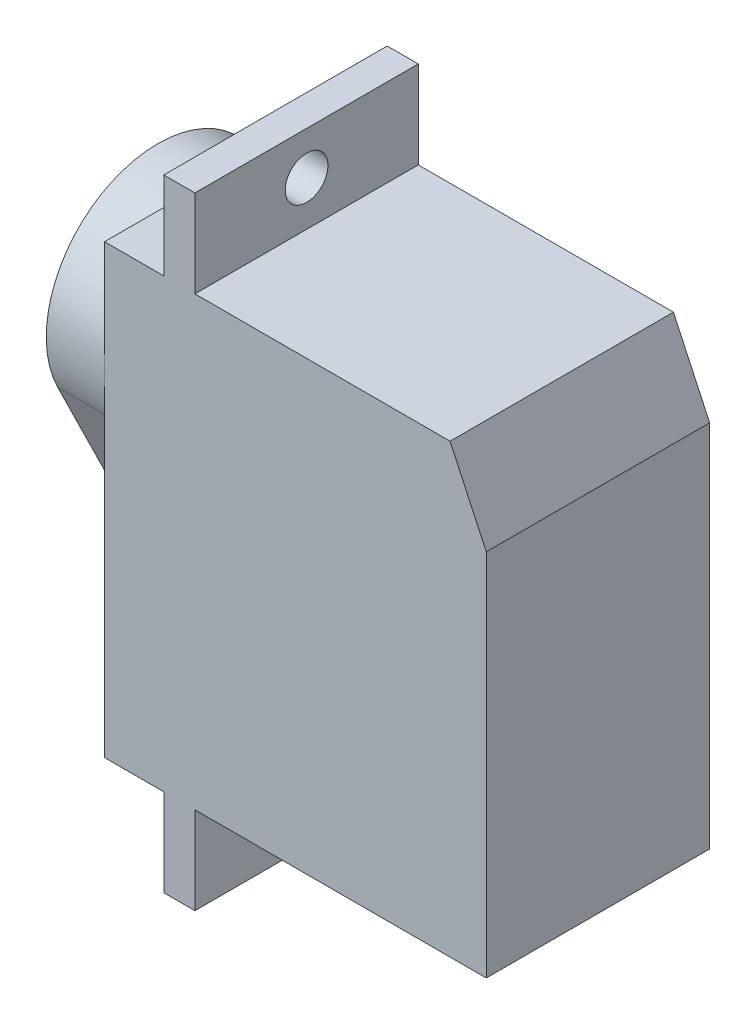
SolidWorks part; units mm, degrees
material "聚亚安酯(11671)"
ref_plane "前视基准面" through (0, 0, 0) normal (0, 0, 1) x (1, 0, 0)
ref_plane "上视基准面" through (0, 0, 0) normal (0, 1, 0) x (1, 0, 0)
ref_plane "右视基准面" through (0, 0, 0) normal (1, 0, 0) x (0, 0, -1)
sketch "草图1" plane through (0, 0, 0) normal (0, 0, 1) x (1, 0, 0)
  line L0 (4.65, 23) -> (4.65, 27.5)
  line L1 (0, 0) -> (3.05, 0)
  line L2 (0, 0) -> (0, 23)
  line L3 (0, 23) -> (3.05, 23)
  line L4 (19.65, 0) -> (19.65, 23)
  line L5 (4.65, -4.5) -> (3.05, -4.5)
  line L6 (4.65, -4.5) -> (4.65, 0)
  line L7 (4.65, 27.5) -> (3.05, 27.5)
  line L8 (3.05, -4.5) -> (3.05, 0)
  line L9 (3.05, 23) -> (3.05, 27.5)
  line L10 (4.65, 0) -> (19.65, 0)
  line L11 (4.65, 23) -> (19.65, 23)
  point P4 (3.85, 11.5)
  dimension "D1" = 19.65
  dimension "D2" = 23
  dimension "D3" = 11.5
  dimension "D4" = 15
  dimension "D5" = 1.6
  dimension "D6" = 32
extrude "凸台-拉伸1" add sketch "草图1" along normal blind 11.5
sketch "草图2" plane through (0, 0, 0) normal (0, 0, 1) x (1, 0, 0)
  line L0 (-4.0495, 11.5) -> (24.7018, 11.5) construction
  line L1 (19.65, 23) -> (4.65, 23) construction
  dimension "D1" = 11.5
sketch "草图3" plane through (3.05, 0, 0) normal (-1, 0, 0) x (0, 0, 1)
  line L0 (11.5, 27.5) -> (11.5, 23) construction
  line L3 (-9.0484, 11.5) -> (22.6748, 11.5) construction
  line L4 (11.5, 23) -> (0, 23) construction
  circle A0 centre (5.75, 25.3) radius 1.1
  dimension "D2" = 11.5
  dimension "D1" = 5.75
  dimension "D3" = 13.8
extrude "切除-拉伸1" cut sketch "草图3" against normal through all
sketch "草图6" plane through (3.05, 0, 0) normal (-1, 0, 0) x (0, 0, 1)
  line L0 (11.5, 23) -> (11.5, 0) construction
  line L1 (11.5, 0) -> (11.5, -4.5) construction
  circle A0 centre (5.75, -2.3) radius 1.1
  point P2 (11.5, 11.5)
  dimension "D1" = 13.8
  dimension "D2" = 5.75
extrude "切除-拉伸2" cut sketch "草图6" against normal through all
sketch "草图7" plane through (0, 0, 0) normal (-1, 0, 0) x (0, 0, 1)
  line L0 (0, 23) -> (0, 0) construction
  line L3 (11.5, 23) -> (0, 23) construction
  circle A0 centre (5.75, 17.25) radius 5.75
sketch "草图8" plane through (0, 0, 0) normal (-1, 0, 0) x (0, 0, 1)
  line L0 (11.5, 23) -> (11.5, 0) construction
  circle A0 centre (5.75, 9.2) radius 1.1
  dimension "D1" = 5.75
  dimension "D2" = 5.75
sketch "草图9" plane through (0, 0, 0) normal (-1, 0, 0) x (0, 0, 1)
  line L0 (-3.3238, 7) -> (18.3056, 7) construction
  dimension "D1" = 10.25
sketch "草图10" plane through (0, 0, 0) normal (-1, 0, 0) x (0, 0, 1)
  line L0 (-3.3238, 7) -> (18.3056, 7) construction
  line L1 (0.5893, 14.7143) -> (3.7755, 8.2298)
  line L2 (7.7245, 8.2298) -> (10.9107, 14.7143)
  arc A1 (3.7755, 8.2298) -> (7.7245, 8.2298) centre (5.75, 9.2) ccw
  circle A2 centre (5.75, 17.25) radius 5.75 construction
  circle A3 centre (5.75, 17.25) radius 5.75
  arc A4 (10.9107, 14.7143) -> (0.5893, 14.7143) centre (5.75, 17.25) ccw
  dimension "D1" = 0
extrude "凸台-拉伸2" add sketch "草图10" along normal blind 3
extrude "凸台-拉伸3" add sketch "草图8" along normal blind 3.6
sketch "草图11" plane through (-3, 0, 0) normal (-1, 0, 0) x (0, 0, 1)
  circle A0 centre (5.75, 17.25) radius 2
extrude "凸台-拉伸4" add sketch "草图11" along normal blind 2
chamfer "倒角1" distance 4 angle 25 1 edges at (19.65, 23, 5.75)
